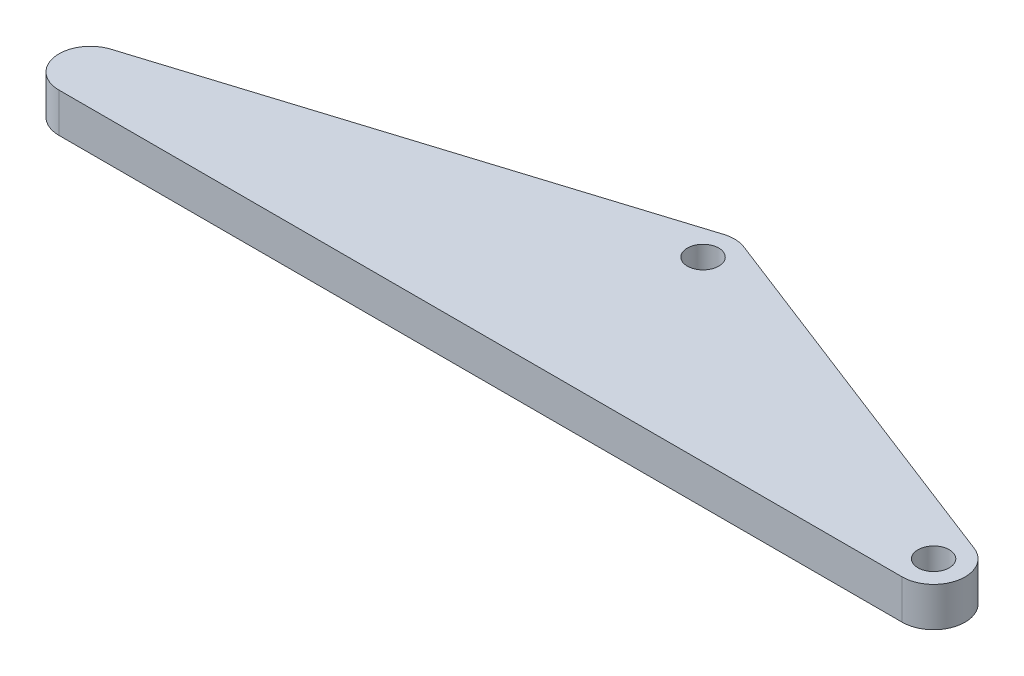
SolidWorks part; units mm, degrees
ref_plane "前视基准面" through (0, 0, 0) normal (0, 0, 1) x (1, 0, 0)
ref_plane "上视基准面" through (0, 0, 0) normal (0, 1, 0) x (1, 0, 0)
ref_plane "右视基准面" through (0, 0, 0) normal (1, 0, 0) x (0, 0, -1)
sketch "草图1" plane through (0, 0, 0) normal (0, 1, 0) x (1, 0, 0)
  line L0 (-53.6685, 0) -> (53.6685, 0) construction
  line L1 (5.7385, 0) -> (5.7385, 18.582) construction
  line L2 (-53.6685, 0) -> (5.7385, 18.582) construction
  line L3 (5.7385, 18.582) -> (53.6685, 0) construction
  line L4 (-53.6685, 0) -> (5.7385, 18.582) construction
  line L5 (-54.8626, 3.8176) -> (4.5444, 22.3996)
  line L6 (-52.4744, -3.8176) -> (6.9326, 14.7644)
  line L7 (5.7385, 18.582) -> (53.6685, 0) construction
  line L8 (7.1844, 22.3115) -> (55.1144, 3.7295)
  line L9 (4.2926, 14.8525) -> (52.2226, -3.7295)
  line L10 (-53.6685, 0) -> (53.6685, 0) construction
  line L11 (-53.6685, 4) -> (53.6685, 4)
  line L12 (-53.6685, -4) -> (53.6685, -4)
  arc A0 (-54.8626, 3.8176) -> (-52.4744, -3.8176) centre (-53.6685, 0) ccw
  arc A1 (6.9326, 14.7644) -> (4.5444, 22.3996) centre (5.7385, 18.582) ccw
  arc A2 (7.1844, 22.3115) -> (4.2926, 14.8525) centre (5.7385, 18.582) ccw
  arc A3 (52.2226, -3.7295) -> (55.1144, 3.7295) centre (53.6685, 0) ccw
  arc A4 (-53.6685, 4) -> (-53.6685, -4) centre (-53.6685, 0) ccw
  arc A5 (53.6685, -4) -> (53.6685, 4) centre (53.6685, 0) ccw
  circle A6 centre (-53.6685, 0) radius 2
  circle A7 centre (5.7385, 18.582) radius 2
  circle A8 centre (53.6685, 0) radius 2
  point P4 (0, 0)
  point P7 (-23.965, 9.291)
  point P12 (29.7035, 9.291)
  point P18 (0, 0)
  dimension "D4" = 4
  dimension "D5" = 4
  dimension "D6" = 4
  dimension "D7" = 4
  dimension "D1" = 107.337
  dimension "D2" = 59.407
  dimension "D3" = 18.582
extrude "凸台-拉伸1" add sketch "草图1" along normal blind 5 contours L11 A4 A0 L6 A6 | A4 L11 L6 L9 A2 L5 | A1 A2 L9 L6 A7 | A5 L8 A1 L6 L9 L11 | A3 L9 L11 L6 A0 L12 | A3 A5 L11 L9 A8 | L6 L11 L9 | A6
